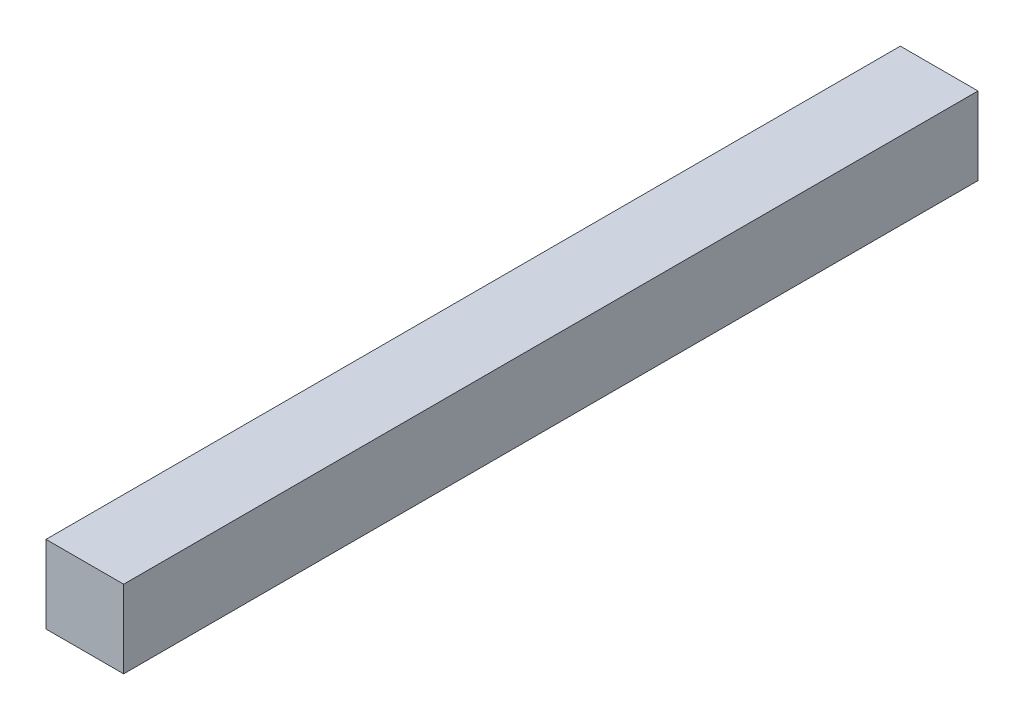
SolidWorks part; units mm, degrees
ref_plane "Front Plane" through (0, 0, 0) normal (0, 0, 1) x (1, 0, 0)
ref_plane "Top Plane" through (0, 0, 0) normal (0, 1, 0) x (1, 0, 0)
ref_plane "Right Plane" through (0, 0, 0) normal (1, 0, 0) x (0, 0, -1)
sketch "Sketch1" plane through (0, 0, 0) normal (0, 0, 1) x (1, 0, 0)
  line L1 (0, 0) -> (-25.4, 0)
  line L2 (0, 0) -> (0, 25.4)
  line L3 (0, 25.4) -> (-25.4, 25.4)
  line L4 (-25.4, 0) -> (-25.4, 25.4)
  dimension "D1" = 25.4
  dimension "D2" = 25.4
extrude "Boss-Extrude1" add sketch "Sketch1" along normal blind 279.4
